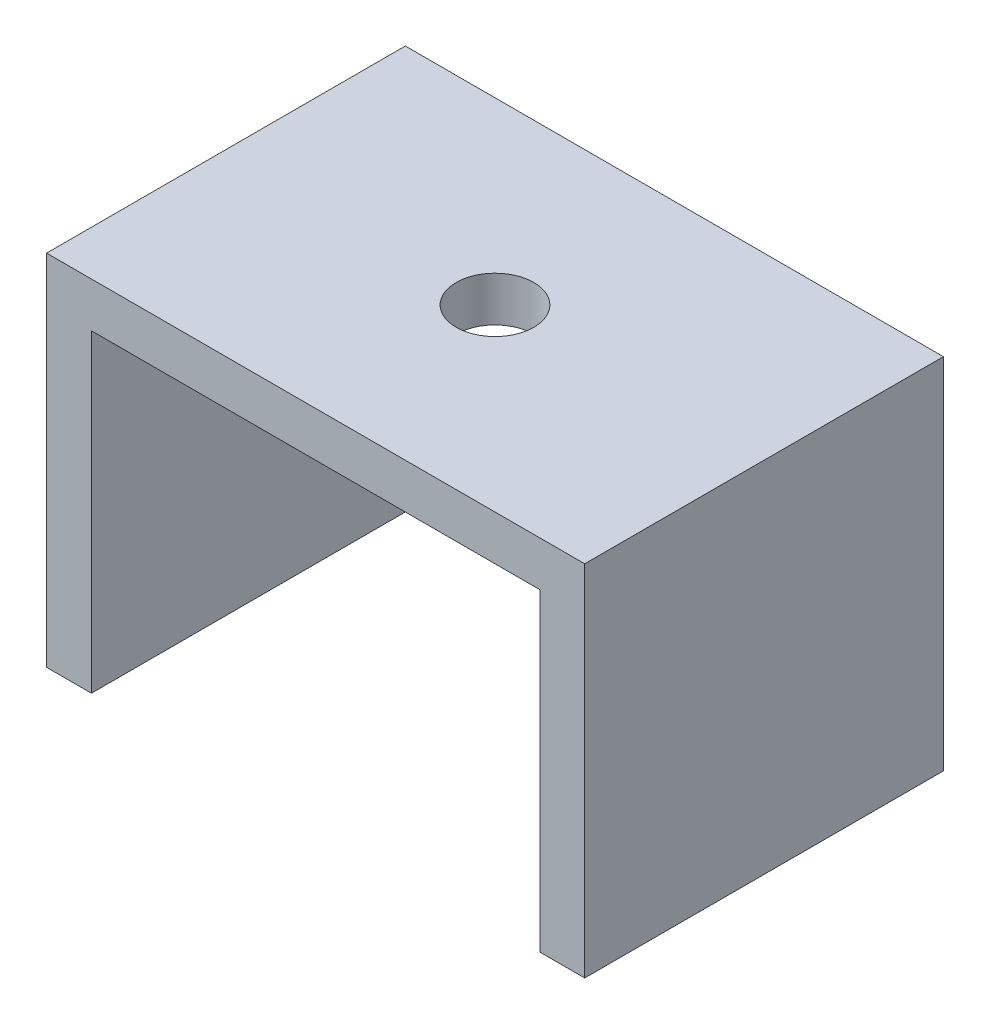
SolidWorks part; units mm, degrees
material "6063-O"
ref_plane "Front" through (0, 0, 0) normal (0, 0, 1) x (1, 0, 0)
ref_plane "Top" through (0, 0, 0) normal (0, 1, 0) x (1, 0, 0)
ref_plane "Right" through (0, 0, 0) normal (1, 0, 0) x (0, 0, -1)
sketch "Sketch1" plane through (0, 0, 0) normal (0, 0, 1) x (1, 0, 0)
  line L0 (0, 0) -> (0, 48916.6043) construction
  line L1 (38.1, 6.35) -> (-38.1, 6.35)
  line L2 (-38.1, 6.35) -> (-38.1, -44.45)
  line L3 (-38.1, -44.45) -> (-31.75, -44.45)
  line L4 (-31.75, -44.45) -> (-31.75, 0)
  line L5 (-31.75, 0) -> (31.75, 0)
  line L6 (38.1, -44.45) -> (31.75, -44.45)
  line L7 (31.75, -44.45) -> (31.75, 0)
  line L8 (38.1, 6.35) -> (38.1, -44.45)
  point P12 (0, 0)
  point P15 (0, 6.35)
  dimension "D1" = 38.1
  dimension "D2" = 31.75
  dimension "D3" = 50.8
  dimension "D4" = 6.35
extrude "Boss-Extrude1" add sketch "Sketch1" along normal blind 50.8
sketch "Sketch2" plane through (0, 6.35, 0) normal (0, 1, 0) x (1, 0, 0)
  line L0 (0, 0) -> (0, -50.8) construction
  line L1 (38.1, -50.8) -> (-38.1, -50.8) construction
  circle A0 centre (0, -25.4) radius 5.5
  dimension "D1" = 11
extrude "Cut-Extrude1" cut sketch "Sketch2" against normal blind 50.8
